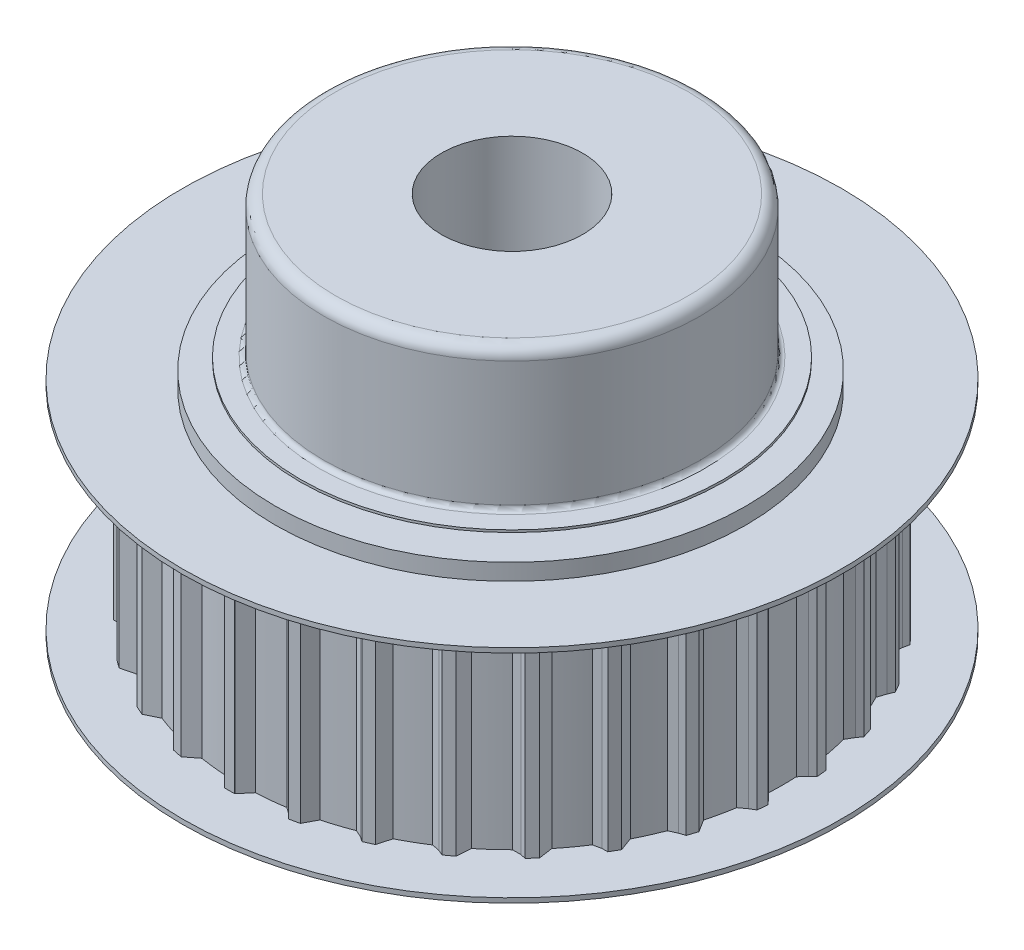
SolidWorks part; units mm, degrees
ref_plane "Plan de face" through (0, 0, 0) normal (0, 0, 1) x (1, 0, 0)
ref_plane "Plan de dessus" through (0, 0, 0) normal (0, 1, 0) x (1, 0, 0)
ref_plane "Plan de droite" through (0, 0, 0) normal (1, 0, 0) x (0, 0, -1)
sketch "Esquisse1" plane through (0, 0, 0) normal (0, 1, 0) x (1, 0, 0)
  circle A0 centre (0, 0) radius 11.5
  dimension "D1" = 23
extrude "Boss.-Extru.1" add sketch "Esquisse1" along normal blind 9
sketch "Esquisse2" plane through (0, 9, 0) normal (0, 1, 0) x (1, 0, 0)
  line L0 (-0.2167, 12) -> (0.215, 12)
  line L1 (0.215, 12) -> (0.65, 11.4816)
  line L2 (-0.65, 11.4816) -> (0.65, 11.4816)
  line L3 (-0.2167, 12) -> (-0.2167, 11.998)
  line L4 (-0.2167, 11.998) -> (-0.65, 11.4816)
  line L6 (2.2786, 11.7796) -> (2.7008, 11.6899)
  line L7 (2.7008, 11.6899) -> (2.7755, 11.46)
  line L8 (2.7755, 11.46) -> (3.0185, 11.0924)
  line L9 (2.2786, 11.7796) -> (2.2782, 11.7777)
  line L10 (2.2782, 11.7777) -> (1.7469, 11.3626)
  line L11 (1.7469, 11.3626) -> (3.0185, 11.0924)
  line L12 (4.6735, 11.0452) -> (5.0679, 10.8697)
  line L13 (5.0679, 10.8697) -> (5.0931, 10.6293)
  line L14 (5.0931, 10.6293) -> (5.2544, 10.2192)
  line L15 (4.6735, 11.0452) -> (4.6727, 11.0435)
  line L16 (4.6727, 11.0435) -> (4.0668, 10.7479)
  line L17 (4.0668, 10.7479) -> (5.2544, 10.2192)
  line L18 (6.8634, 9.829) -> (7.2126, 9.5752)
  line L19 (7.2126, 9.5752) -> (7.2157, 9.3143)
  line L20 (7.2157, 9.3143) -> (7.2598, 8.9002)
  line L21 (6.8634, 9.829) -> (6.8622, 9.8274)
  line L22 (6.8622, 9.8274) -> (6.2081, 9.6643)
  line L23 (6.2081, 9.6643) -> (7.2598, 8.9002)
  line L24 (8.7525, 8.184) -> (9.0414, 7.8632)
  line L25 (9.0414, 7.8632) -> (8.9901, 7.6073)
  line L26 (8.9901, 7.6073) -> (8.9472, 7.1931)
  line L27 (8.7525, 8.184) -> (8.7511, 8.1827)
  line L28 (8.7511, 8.1827) -> (8.0773, 8.1592)
  line L29 (8.0773, 8.1592) -> (8.9472, 7.1931)
  line L30 (10.2584, 6.1822) -> (10.4743, 5.8083)
  line L31 (10.4743, 5.8083) -> (10.3709, 5.5687)
  line L32 (10.3709, 5.5687) -> (10.2428, 5.1725)
  line L33 (10.2584, 6.1822) -> (10.2567, 6.1812)
  line L34 (10.2567, 6.1812) -> (9.5928, 6.2983)
  line L35 (9.5928, 6.2983) -> (10.2428, 5.1725)
  line L36 (11.3152, 3.9111) -> (11.4486, 3.5005)
  line L37 (11.4486, 3.5005) -> (11.2976, 3.2876)
  line L38 (11.2976, 3.2876) -> (11.09, 2.9266)
  line L39 (11.3152, 3.9111) -> (11.3133, 3.9104)
  line L40 (11.3133, 3.9104) -> (10.6882, 4.163)
  line L41 (10.6882, 4.163) -> (11.09, 2.9266)
  line L42 (11.8766, 1.4698) -> (11.9218, 1.0405)
  line L43 (11.9218, 1.0405) -> (11.7299, 0.8636)
  line L44 (11.7299, 0.8636) -> (11.4517, 0.5537)
  line L45 (11.8766, 1.4698) -> (11.8747, 1.4696)
  line L46 (11.8747, 1.4696) -> (11.3158, 1.8466)
  line L47 (11.3158, 1.8466) -> (11.4517, 0.5537)
  line L48 (11.9183, -1.0348) -> (11.8732, -1.4641)
  line L49 (11.8732, -1.4641) -> (11.6487, -1.5972)
  line L50 (11.6487, -1.5972) -> (11.3121, -1.8425)
  line L51 (11.9183, -1.0348) -> (11.9163, -1.0346)
  line L52 (11.9163, -1.0346) -> (11.448, -0.5497)
  line L53 (11.448, -0.5497) -> (11.3121, -1.8425)
  line L54 (11.4383, -3.4934) -> (11.3049, -3.9039)
  line L55 (11.3049, -3.9039) -> (11.0576, -3.9874)
  line L56 (11.0576, -3.9874) -> (10.6774, -4.1574)
  line L57 (11.4383, -3.4934) -> (11.4364, -3.4927)
  line L58 (11.4364, -3.4927) -> (11.0792, -2.921)
  line L59 (11.0792, -2.921) -> (10.6774, -4.1574)
  line L60 (10.4576, -5.7984) -> (10.2417, -6.1722)
  line L61 (10.2417, -6.1722) -> (10, -6.1722)
  line L62 (10, -6.1722) -> (9.5928, -6.2594)
  line L63 (10.4576, -5.7984) -> (10.4559, -5.7974)
  line L64 (10.4559, -5.7974) -> (10.2253, -5.1639)
  line L65 (10.2253, -5.1639) -> (9.5928, -6.2594)
  line L66 (9.0191, -7.8491) -> (8.7302, -8.1699)
  line L67 (8.7302, -8.1699) -> (8.4938, -8.1197)
  line L68 (8.4938, -8.1197) -> (8.0773, -8.1203)
  line L69 (9.0191, -7.8491) -> (9.0176, -7.8478)
  line L70 (9.0176, -7.8478) -> (8.9238, -7.1802)
  line L71 (8.9238, -7.1802) -> (8.0773, -8.1203)
  line L72 (7.1857, -9.556) -> (6.8364, -9.8097)
  line L73 (6.8364, -9.8097) -> (6.6156, -9.7114)
  line L74 (6.6156, -9.7114) -> (6.2081, -9.6255)
  line L75 (7.1857, -9.556) -> (7.1845, -9.5544)
  line L76 (7.1845, -9.5544) -> (7.2315, -8.8819)
  line L77 (7.2315, -8.8819) -> (6.2081, -9.6255)
  line L78 (5.0374, -10.8444) -> (4.643, -11.02)
  line L79 (4.643, -11.02) -> (4.4475, -10.8779)
  line L80 (4.4475, -10.8779) -> (4.0668, -10.7091)
  line L81 (5.0374, -10.8444) -> (5.0366, -10.8426)
  line L82 (5.0366, -10.8426) -> (5.2224, -10.1945)
  line L83 (5.2224, -10.1945) -> (4.0668, -10.7091)
  line L84 (2.6682, -11.6579) -> (2.246, -11.7477)
  line L85 (2.246, -11.7477) -> (2.0842, -11.5681)
  line L86 (2.0842, -11.5681) -> (1.7469, -11.3238)
  line L87 (2.6682, -11.6579) -> (2.6678, -11.656)
  line L88 (2.6678, -11.656) -> (2.9843, -11.0608)
  line L89 (2.9843, -11.0608) -> (1.7469, -11.3238)
  line L90 (0.1817, -11.9612) -> (-0.25, -11.9612)
  line L91 (-0.25, -11.9612) -> (-0.3709, -11.7518)
  line L92 (-0.3709, -11.7518) -> (-0.65, -11.4428)
  line L93 (0.1817, -11.9612) -> (0.1817, -11.9592)
  line L94 (0.1817, -11.9592) -> (0.615, -11.4428)
  line L95 (0.615, -11.4428) -> (-0.65, -11.4428)
  line L96 (-2.3136, -11.7408) -> (-2.7358, -11.651)
  line L97 (-2.7358, -11.651) -> (-2.8105, -11.4211)
  line L98 (-2.8105, -11.4211) -> (-3.0193, -11.0608)
  line L99 (-2.3136, -11.7408) -> (-2.3132, -11.7388)
  line L100 (-2.3132, -11.7388) -> (-1.7819, -11.3238)
  line L101 (-1.7819, -11.3238) -> (-3.0193, -11.0608)
  line L102 (-4.7085, -11.0064) -> (-5.1028, -10.8308)
  line L103 (-5.1028, -10.8308) -> (-5.1281, -10.5904)
  line L104 (-5.1281, -10.5904) -> (-5.2574, -10.1945)
  line L105 (-4.7085, -11.0064) -> (-4.7077, -11.0046)
  line L106 (-4.7077, -11.0046) -> (-4.1018, -10.7091)
  line L107 (-4.1018, -10.7091) -> (-5.2574, -10.1945)
  line L108 (-6.8984, -9.7901) -> (-7.2476, -9.5364)
  line L109 (-7.2476, -9.5364) -> (-7.2223, -9.296)
  line L110 (-7.2223, -9.296) -> (-7.2665, -8.8819)
  line L111 (-6.8984, -9.7901) -> (-6.8972, -9.7886)
  line L112 (-6.8972, -9.7886) -> (-6.2431, -9.6255)
  line L113 (-6.2431, -9.6255) -> (-7.2665, -8.8819)
  line L114 (-8.7875, -8.1452) -> (-9.0764, -7.8244)
  line L115 (-9.0764, -7.8244) -> (-9.0017, -7.5945)
  line L116 (-9.0017, -7.5945) -> (-8.9588, -7.1802)
  line L117 (-8.7875, -8.1452) -> (-8.7861, -8.1439)
  line L118 (-8.7861, -8.1439) -> (-8.1123, -8.1203)
  line L119 (-8.1123, -8.1203) -> (-8.9588, -7.1802)
  line L120 (-10.2934, -6.1434) -> (-10.5092, -5.7695)
  line L121 (-10.5092, -5.7695) -> (-10.3884, -5.5602)
  line L122 (-10.3884, -5.5602) -> (-10.2603, -5.1639)
  line L123 (-10.2934, -6.1434) -> (-10.2917, -6.1424)
  line L124 (-10.2917, -6.1424) -> (-9.6278, -6.2594)
  line L125 (-9.6278, -6.2594) -> (-10.2603, -5.1639)
  line L126 (-11.3501, -3.8722) -> (-11.4835, -3.4616)
  line L127 (-11.4835, -3.4616) -> (-11.3218, -3.282)
  line L128 (-11.3218, -3.282) -> (-11.1141, -2.921)
  line L129 (-11.3501, -3.8722) -> (-11.3483, -3.8716)
  line L130 (-11.3483, -3.8716) -> (-10.7232, -4.1241)
  line L131 (-10.7232, -4.1241) -> (-11.1141, -2.921)
  line L132 (-11.9116, -1.431) -> (-11.9567, -1.0017)
  line L133 (-11.9567, -1.0017) -> (-11.7612, -0.8596)
  line L134 (-11.7612, -0.8596) -> (-11.483, -0.5497)
  line L135 (-11.9116, -1.431) -> (-11.9097, -1.4308)
  line L136 (-11.9097, -1.4308) -> (-11.3508, -1.8078)
  line L137 (-11.3508, -1.8078) -> (-11.483, -0.5497)
  line L138 (-11.9533, 1.0736) -> (-11.9081, 1.503)
  line L139 (-11.9081, 1.503) -> (-11.6873, 1.6013)
  line L140 (-11.6873, 1.6013) -> (-11.3508, 1.8466)
  line L141 (-11.9533, 1.0736) -> (-11.9513, 1.0734)
  line L142 (-11.9513, 1.0734) -> (-11.483, 0.5885)
  line L143 (-11.483, 0.5885) -> (-11.3508, 1.8466)
  line L144 (-11.4732, 3.5322) -> (-11.3398, 3.9428)
  line L145 (-11.3398, 3.9428) -> (-11.1034, 3.993)
  line L146 (-11.1034, 3.993) -> (-10.7124, 4.1963)
  line L147 (-11.4732, 3.5322) -> (-11.4714, 3.5316)
  line L148 (-11.4714, 3.5316) -> (-11.1141, 2.9599)
  line L149 (-11.1141, 2.9599) -> (-10.7124, 4.1963)
  line L150 (-10.4926, 5.8372) -> (-10.2767, 6.2111)
  line L151 (-10.2767, 6.2111) -> (-10.035, 6.2111)
  line L152 (-10.035, 6.2111) -> (-9.6103, 6.3286)
  line L153 (-10.4926, 5.8372) -> (-10.4909, 5.8362)
  line L154 (-10.4909, 5.8362) -> (-10.2603, 5.2027)
  line L155 (-10.2603, 5.2027) -> (-9.6103, 6.3286)
  line L156 (-9.0541, 7.888) -> (-8.7652, 8.2088)
  line L157 (-8.7652, 8.2088) -> (-8.5288, 8.1585)
  line L158 (-8.5288, 8.1585) -> (-8.0889, 8.1852)
  line L159 (-9.0541, 7.888) -> (-9.0526, 7.8867)
  line L160 (-9.0526, 7.8867) -> (-8.9588, 7.2191)
  line L161 (-8.9588, 7.2191) -> (-8.0889, 8.1852)
  line L162 (-7.2206, 9.5948) -> (-6.8714, 9.8486)
  line L163 (-6.8714, 9.8486) -> (-6.6506, 9.7503)
  line L164 (-6.6506, 9.7503) -> (-6.2148, 9.6849)
  line L165 (-7.2206, 9.5948) -> (-7.2195, 9.5933)
  line L166 (-7.2195, 9.5933) -> (-7.2665, 8.9208)
  line L167 (-7.2665, 8.9208) -> (-6.2148, 9.6849)
  line L168 (-5.0724, 10.8832) -> (-4.678, 11.0588)
  line L169 (-4.678, 11.0588) -> (-4.4825, 10.9167)
  line L170 (-4.4825, 10.9167) -> (-4.0698, 10.7621)
  line L171 (-5.0724, 10.8832) -> (-5.0716, 10.8814)
  line L172 (-5.0716, 10.8814) -> (-5.2574, 10.2334)
  line L173 (-5.2574, 10.2334) -> (-4.0698, 10.7621)
  line L174 (-2.7032, 11.6968) -> (-2.281, 11.7865)
  line L175 (-2.281, 11.7865) -> (-2.1192, 11.6069)
  line L176 (-2.1192, 11.6069) -> (-1.7477, 11.3699)
  line L177 (-2.7032, 11.6968) -> (-2.7028, 11.6949)
  line L178 (-2.7028, 11.6949) -> (-3.0193, 11.0996)
  line L179 (-3.0193, 11.0996) -> (-1.7477, 11.3699)
  circle A0 centre (0, 0) radius 11.5 construction
  point P9 (-0.2039, 12)
  point P269 (-0.0175, 0.0194)
  dimension "D4" = 130
  dimension "D2" = 12
  dimension "D3" = 0
  dimension "D5" = 12
  dimension "D6" = 130
  dimension "D7" = 0.4317
  dimension "D8" = 0.4333
  dimension "D9" = 0.435
  dimension "D10" = 30
extrude "Boss.-Extru.3" add sketch "Esquisse2" against normal blind 9
sketch "Esquisse3" plane through (0, 9, 0) normal (0, 1, 0) x (1, 0, 0)
  circle A0 centre (0, 0) radius 14
  dimension "D1" = 28
extrude "Boss.-Extru.4" add sketch "Esquisse3" along normal blind 0.2
sketch "Esquisse4" plane through (0, 9.2, 0) normal (0, 1, 0) x (1, 0, 0)
  circle A0 centre (0.3577, -0.4174) radius 10
  dimension "D1" = 20
extrude "Boss.-Extru.5" add sketch "Esquisse4" along normal blind 0.7
sketch "Esquisse5" plane through (0, 9.9, 0) normal (0, 1, 0) x (1, 0, 0)
  circle A0 centre (0, 0) radius 9
  dimension "D1" = 18
extrude "Boss.-Extru.6" add sketch "Esquisse5" along normal blind 0.1
sketch "Esquisse6" plane through (0, 0, 0) normal (0, -1, 0) x (1, 0, 0)
  circle A0 centre (0, 0) radius 14
  dimension "D1" = 28
extrude "Boss.-Extru.7" add sketch "Esquisse6" along normal blind 0.2
sketch "Esquisse7" plane through (0, -0.2, 0) normal (0, -1, 0) x (-1, 0, 0)
  circle A0 centre (0, 0) radius 10
  dimension "D1" = 20
extrude "Boss.-Extru.8" add sketch "Esquisse7" along normal blind 0.7
sketch "Esquisse8" plane through (0, -0.9, 0) normal (0, -1, 0) x (-1, 0, 0)
  circle A0 centre (0, 0) radius 9
  dimension "D1" = 18
extrude "Boss.-Extru.9" add sketch "Esquisse8" along normal blind 0.1
sketch "Esquisse9" plane through (0, 10, 0) normal (0, 1, 0) x (1, 0, 0)
  circle A0 centre (0, 0) radius 8
  dimension "D1" = 16
extrude "Boss.-Extru.10" add sketch "Esquisse9" along normal blind 6
fillet "Congé1" radius 0.5 1 edges at (0, 16, 8)
fillet "Congé2" radius 0.2 1 edges at (0, 10, 8)
sketch "Esquisse10" plane through (0, 16, 0) normal (0, 1, 0) x (1, 0, 0)
  circle A0 centre (0, 0) radius 3
  dimension "D1" = 6
extrude "Enlèv. mat.-Extru.1" cut sketch "Esquisse10" against normal through all
